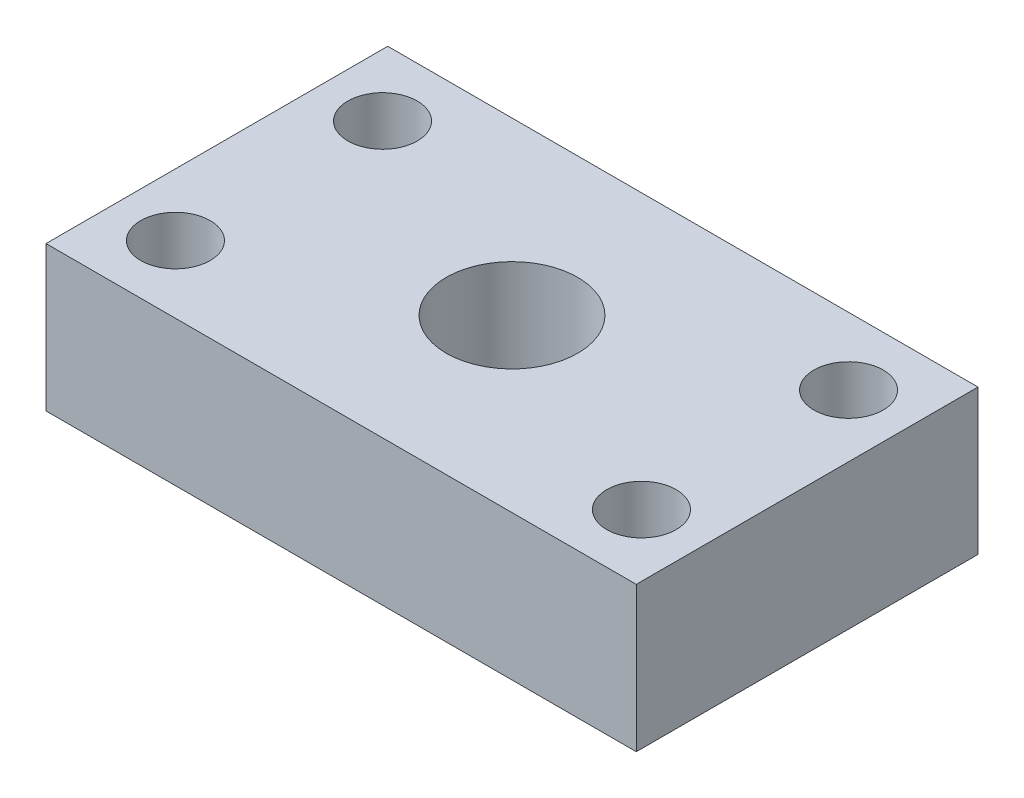
SolidWorks part; units mm, degrees
ref_plane "Front Plane" through (0, 0, 0) normal (0, 0, 1) x (1, 0, 0)
ref_plane "Top Plane" through (0, 0, 0) normal (0, 1, 0) x (1, 0, 0)
ref_plane "Right Plane" through (0, 0, 0) normal (1, 0, 0) x (0, 0, -1)
sketch "Sketch1" plane through (0, 0, 0) normal (0, 1, 0) x (1, 0, 0)
  line L1 (0, 0) -> (57, 0)
  line L2 (0, 0) -> (0, 33)
  line L3 (0, 33) -> (57, 33)
  line L4 (57, 0) -> (57, 33)
  dimension "D1" = 33
  dimension "D2" = 57
extrude "Boss-Extrude1" add sketch "Sketch1" along normal blind 14
sketch "Sketch3" plane through (0, 0, 0) normal (0, -1, 0) x (1, 0, 0)
  line L2 (0, 0) -> (57, 0) construction
  line L3 (0, -33) -> (0, 0) construction
  circle A0 centre (6, -6.5) radius 3.35
  point P4 (28.5, 0)
  point P9 (0, -16.5)
  dimension "D1" = 22.5
  dimension "D3" = 6.7
  dimension "D2" = 10
extrude "Cut-Extrude1" cut sketch "Sketch3" against normal through all
sketch "Sketch4" plane through (0, 0, 0) normal (0, -1, 0) x (1, 0, 0)
  line L2 (57, 0) -> (57, -33) construction
  line L3 (57, -33) -> (0, -33) construction
  circle A0 centre (51, -26.5) radius 3.35
  point P5 (57, -16.5)
  point P10 (28.5, -33)
  dimension "D1" = 10
  dimension "D3" = 6.7
  dimension "D2" = 22.5
extrude "Cut-Extrude2" cut sketch "Sketch4" against normal through all
ref_plane "Plane1" through (0, 0, 0) normal (1, 0, 0) x (0, 0, -1)
sketch "Sketch10" plane through (0, 0, 0) normal (0, -1, 0) x (1, 0, 0)
  line L2 (57, -33) -> (0, -33) construction
  line L3 (57, 0) -> (57, -33) construction
  circle A0 centre (6, -26.5) radius 3.35
  point P5 (28.5, -33)
  point P8 (57, -16.5)
  dimension "D1" = 22.5
  dimension "D3" = 6.7
  dimension "D2" = 10
extrude "Cut-Extrude5" cut sketch "Sketch10" against normal through all
sketch "Sketch12" plane through (0, 0, 0) normal (0, -1, 0) x (1, 0, 0)
  line L2 (57, 0) -> (57, -33) construction
  line L3 (0, 0) -> (57, 0) construction
  circle A0 centre (51, -6.5) radius 3.35
  point P5 (57, -16.5)
  point P10 (28.5, 0)
  dimension "D3" = 6.7
  dimension "D1" = 10
  dimension "D2" = 22.5
extrude "Cut-Extrude6" cut sketch "Sketch12" against normal through all
sketch "Sketch13" plane through (0, 0, -33) normal (0, 0, -1) x (-1, 0, 0)
  line L0 (-28.5, 14) -> (-28.5, 0) construction
  line L1 (-57, 14) -> (0, 14) construction
  line L2 (-57, 0) -> (0, 0) construction
  line L3 (-57, 7) -> (0, 7) construction
  line L4 (-57, 14) -> (-57, 0) construction
hole_wizard "#8-32 Tapped Hole1" positions "Sketch14" profile "Sketch15" tap size "#8-32" standard "ANSI Inch"
sketch "Sketch14" plane through (0, 0, -33) normal (0, 0, -1) x (-1, 0, 0)
  line L0 (-57, 7) -> (0, 7) construction
  line L1 (-28.5, 14) -> (-28.5, 0) construction
  point P0 (-28.5, 7)
  dimension "D1" = 0
  dimension "D2" = 0
sketch "Sketch15" plane through (28.5, 7, -33) normal (1, 0, 0) x (0, 1, 0)
  line L0 (0, 0) -> (0, 6.0378)
  line L1 (0, 6.0378) -> (1.7272, 5)
  line L2 (1.7272, 5) -> (1.7272, 0)
  line L5 (1.7272, 0) -> (0, 0)
  line L10 (0, 6.0378) -> (-1.7272, 5) construction
  line L11 (0, -6.35) -> (0, 107.95) construction
  dimension "Tap Drill Dia." = 3.4544
  dimension "Tap Drill Depth" = 5
  dimension "Drill Angle" = 118
cosmetic thread "Hole Thread1" parameters "D1"=5, "D2"=4.1656
hole_wizard "0.535-40 Tapped Hole1" positions "Sketch19" profile "Sketch18" tap size "0.535-40" standard "Thorlabs" end condition through all
sketch "Sketch19" plane through (0, 14, 0) normal (0, 1, 0) x (1, 0, 0)
  line L1 (57, 0) -> (57, 33) construction
  line L2 (28.5, 33) -> (28.5, 0) construction
  line L3 (57, 33) -> (0, 33) construction
  line L4 (0, 0) -> (57, 0) construction
  line L6 (57, 16.5) -> (0, 16.5) construction
  line L7 (0, 33) -> (0, 0) construction
  point P0 (28.5, 16.5)
  point P5 (57, 16.5)
  dimension "D1" = 0
  dimension "D2" = 0
cosmetic thread "Hole Thread3" parameters "D2"=13.589
sketch "Sketch18" plane through (28.5, 14, -16.5) normal (1, 0, 0) x (0, 0, 1)
  line L0 (0, 0) -> (0, 14)
  line L1 (0, 14) -> (6.35, 14)
  line L2 (6.35, 14) -> (6.35, 0)
  line L5 (6.35, 0) -> (0, 0)
  line L11 (0, -6.35) -> (0, 107.95) construction
  dimension "Thru Tap Drill Dia." = 12.7
  dimension "Thru Tap Drill Depth" = 14
